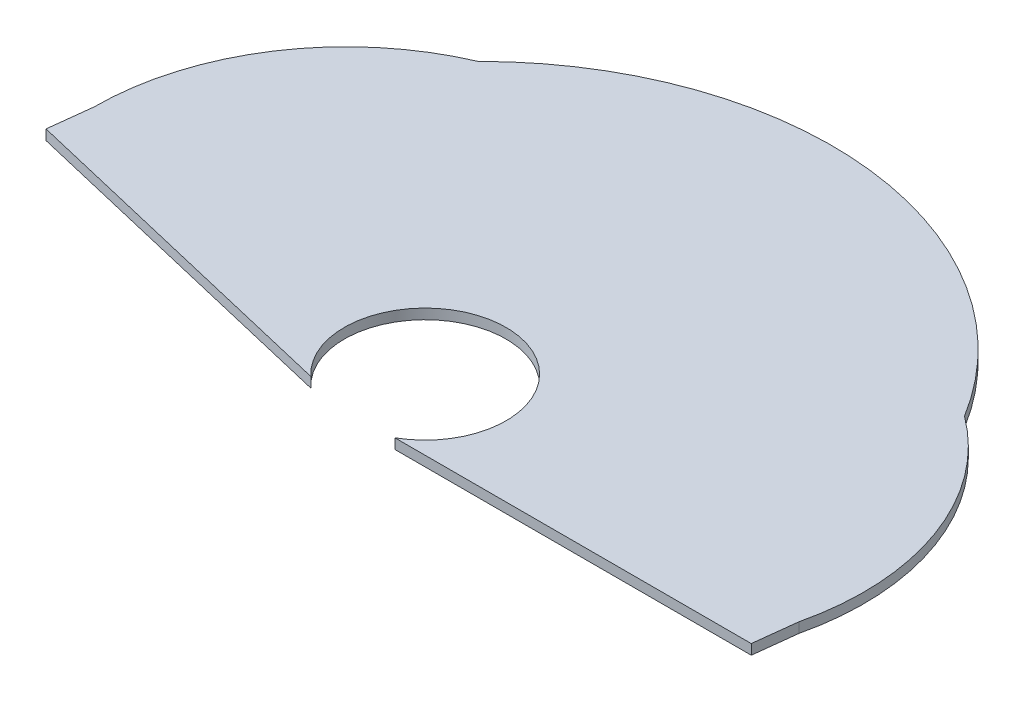
SolidWorks part; units mm, degrees
ref_plane "Alzado" through (0, 0, 0) normal (0, 0, 1) x (1, 0, 0)
ref_plane "Planta" through (0, 0, 0) normal (0, 1, 0) x (1, 0, 0)
ref_plane "Vista lateral" through (0, 0, 0) normal (1, 0, 0) x (0, 0, -1)
sketch "Croquis2" plane through (0, 0, 0) normal (0, 1, 0) x (1, 0, 0)
  line L0 (0, 0) -> (20, 0)
  line L1 (20, 0) -> (39.4636, -4.601)
  arc A0 (7.548, 11.4575) -> (0, 0) centre (12.47, 0) ccw
  arc A1 (39.4636, -4.601) -> (34.7538, 8.2856) centre (27.328, -1.7323) ccw
  arc A2 (7.548, 11.4575) -> (34.7538, 8.2856) centre (19.9028, -0.8339) cw
  dimension "D6" = 24.94
  dimension "D7" = 24.94
  dimension "D1" = 20
  dimension "D2" = 20
  dimension "D3" = 166.7
  dimension "D4" = 7.53
  dimension "D5" = 7.53
extrude "Saliente-Extruir2" add sketch "Croquis2" along normal blind 0.5
sketch "Croquis3" plane through (0, 0.5, 0) normal (0, 1, 0) x (1, 0, 0)
  line L0 (20, 0) -> (16.5, 0)
  line L1 (0, 0) -> (20, 0) construction
  line L2 (20, 0) -> (23.4061, -0.8052)
  line L3 (20, 0) -> (39.4636, -4.601) construction
  arc A1 (16.5, 0) -> (23.4061, -0.8052) centre (19.6222, -3.2407) cw
  dimension "D1" = 3.5
  dimension "D3" = 4.5
  dimension "D2" = 3.5
extrude "Cortar-Extruir1" cut sketch "Croquis3" against normal blind 0.5
sketch "Croquis4" plane through (0, 0.5, 0) normal (0, 1, 0) x (1, 0, 0)
  line L0 (20.1433, 1.229) -> (19.6222, -3.2407) construction
  line L1 (19.6222, -3.2407) -> (19.2169, -6.7171) construction
  line L2 (19.2169, -6.7171) -> (-0.2467, -2.1161)
  line L3 (19.2169, -6.7171) -> (39.2169, -6.7171)
  line L4 (0, 0) -> (-0.2467, -2.1161)
  line L5 (39.4636, -4.601) -> (39.2169, -6.7171)
  line L6 (0, 0) -> (20.6906, 2.9042)
  line L7 (20.6906, 2.9042) -> (39.4636, -4.601)
  arc A0 (23.4061, -0.8052) -> (16.5, 0) centre (19.6222, -3.2407) ccw construction
  circle A1 centre (19.6222, -3.2407) radius 3.5 construction
  circle A2 centre (19.6222, -3.2407) radius 4
  arc M1 (16.5, 0) -> (23.4061, -0.8052) centre (19.6222, -3.2407) cw
  line M2 (23.4061, -0.8052) -> (39.4636, -4.601)
  line M6 (0, 0) -> (16.5, 0)
  dimension "D1" = 7
  dimension "D6" = 8
  dimension "D2" = 166.7
  dimension "D3" = 83.35
  dimension "D4" = 20
  dimension "D5" = 20
  dimension "D7" = 4.5
extrude "Saliente-Extruir3" add sketch "Croquis4" against normal blind 0.5 contours A2 L3 L5 L4 L2 M2 M1 M6 | L7 L6 M6 M1 M2
